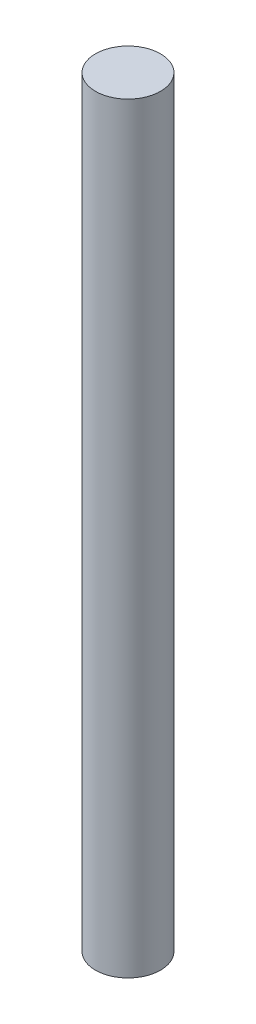
SolidWorks part; units mm, degrees
material "Chrome Stainless Steel"
ref_plane "Front Plane" through (0, 0, 0) normal (0, 0, 1) x (1, 0, 0)
ref_plane "Top Plane" through (0, 0, 0) normal (0, 1, 0) x (1, 0, 0)
ref_plane "Right Plane" through (0, 0, 0) normal (1, 0, 0) x (0, 0, -1)
sketch "Sketch1" plane through (0, 0, 0) normal (0, 1, 0) x (1, 0, 0)
  circle A0 centre (0, 0) radius 3.175
  dimension "D1" = 6.35
extrude "Boss-Extrude1" add sketch "Sketch1" along normal blind 74.295
